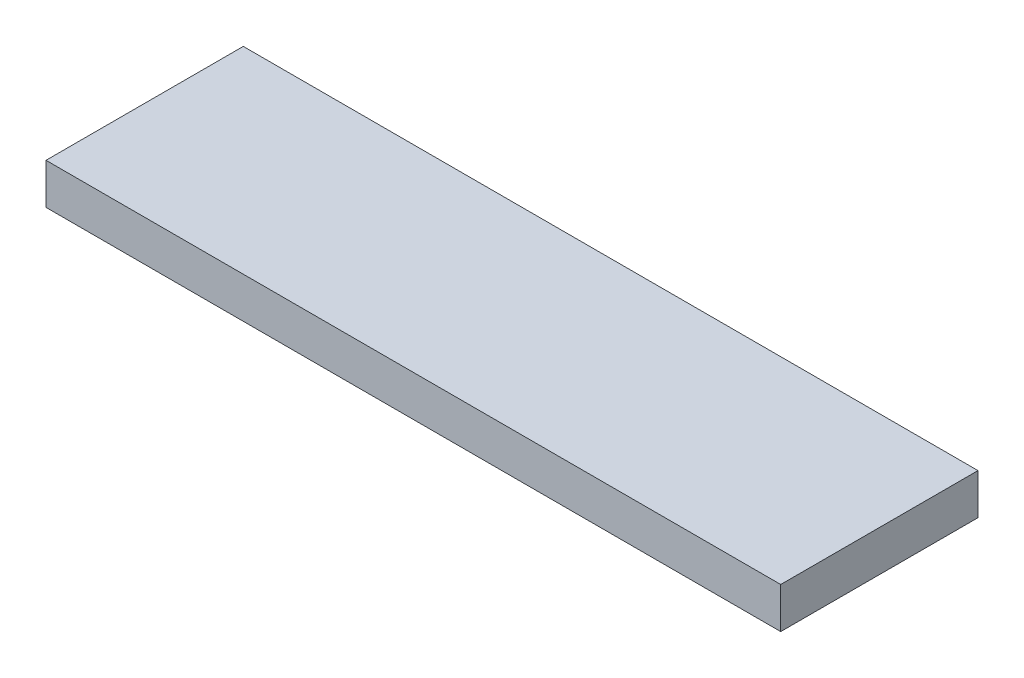
SolidWorks part; units mm, degrees
material "Pine"
ref_plane "Front Plane" through (0, 0, 0) normal (0, 0, 1) x (1, 0, 0)
ref_plane "Top Plane" through (0, 0, 0) normal (0, 1, 0) x (1, 0, 0)
ref_plane "Right Plane" through (0, 0, 0) normal (1, 0, 0) x (0, 0, -1)
sketch "Sketch1" plane through (0, 0, 0) normal (0, 1, 0) x (1, 0, 0)
  line L1 (0, 0) -> (685.8, 0)
  line L2 (0, 0) -> (0, 184.15)
  line L3 (0, 184.15) -> (685.8, 184.15)
  line L4 (685.8, 0) -> (685.8, 184.15)
  dimension "D1" = 184.15
  dimension "D2" = 685.8
extrude "Boss-Extrude1" add sketch "Sketch1" along normal blind 38.1
